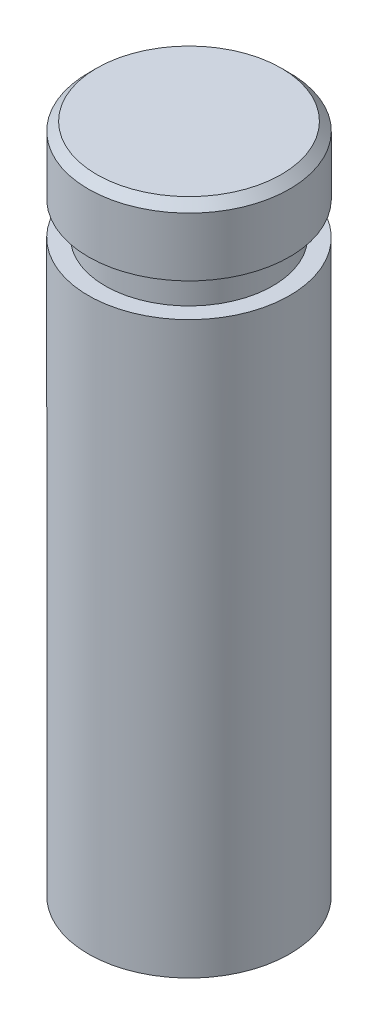
SolidWorks part; units mm, degrees
ref_plane "Plano frontal" through (0, 0, 0) normal (0, 0, 1) x (1, 0, 0)
ref_plane "Plano superior" through (0, 0, 0) normal (0, 1, 0) x (1, 0, 0)
ref_plane "Plano direito" through (0, 0, 0) normal (1, 0, 0) x (0, 0, -1)
sketch "Esboço1" plane through (0, 0, 0) normal (0, 1, 0) x (1, 0, 0)
  circle A0 centre (0, 0) radius 6
  dimension "D1" = 12
extrude "Extrusão1" add sketch "Esboço1" along normal blind 40
sketch "Esboço2" plane through (0, 0, 0) normal (0, -1, 0) x (1, 0, 0)
  circle A0 centre (0, 0) radius 5
  dimension "D1" = 10
extrude "Corte-extrusão1" cut sketch "Esboço2" against normal blind 30
chamfer "Chanfro1" distance 0.5 angle 45 1 edges at (0, 40, 6)
sketch "Esboço3" plane through (0, 0, 0) normal (0, 0, 1) x (1, 0, 0)
  line L0 (0, 0) -> (0, 42.9305) construction
  line L1 (5.5, 40) -> (-5.5, 40) construction
  line L2 (5, 36) -> (8, 36)
  line L3 (5, 36) -> (5, 34)
  line L4 (5, 34) -> (8, 34)
  line L5 (8, 36) -> (8, 34)
  dimension "D1" = 2
  dimension "D2" = 4
  dimension "D3" = 3
  dimension "D4" = 8
revolve "Corte-Revolução3" cut sketch "Esboço3" angle 360 about L0
